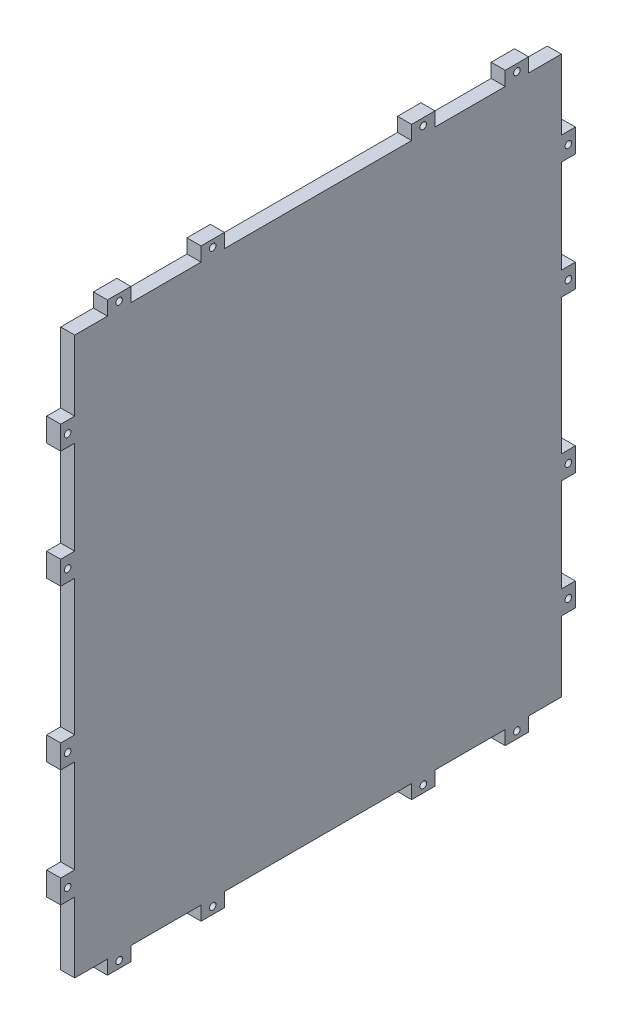
SolidWorks part; units mm, degrees
ref_plane "Plan de face" through (0, 0, 0) normal (0, 0, 1) x (1, 0, 0)
ref_plane "Plan de dessus" through (0, 0, 0) normal (0, 1, 0) x (1, 0, 0)
ref_plane "Plan de droite" through (0, 0, 0) normal (1, 0, 0) x (0, 0, -1)
sketch "Esquisse1" plane through (0, 0, 0) normal (1, 0, 0) x (0, 0, -1)
  line L0 (97.1531, 0) -> (-102.2664, 0) construction
  line L1 (-104, 119) -> (104, 119)
  line L2 (-104, 119) -> (-104, -119)
  line L3 (-104, -119) -> (104, -119)
  line L4 (104, 119) -> (104, -119)
  line L5 (0, 70.2098) -> (0, -91.4498) construction
  dimension "D1" = 238
  dimension "D2" = 208
  dimension "D3" = 104
  dimension "D4" = 119
extrude "Boss.-Extru.1" add sketch "Esquisse1" along normal blind 6
sketch "Esquisse3" plane through (6, 0, 0) normal (1, 0, 0) x (0, 0, -1)
  line L0 (-104, -119) -> (104, -119) construction
  line L1 (-90, -119) -> (-80, -119)
  line L2 (-90, -119) -> (-90, -125)
  line L3 (-90, -125) -> (-80, -125)
  line L4 (-80, -119) -> (-80, -125)
  line L5 (245.3741, 0) -> (-166.5298, 0) construction
  line L6 (-40, -119) -> (-50, -119)
  line L7 (-40, -119) -> (-40, -125)
  line L8 (-40, -125) -> (-50, -125)
  line L9 (-50, -119) -> (-50, -125)
  line L10 (0, 208.6671) -> (0, -232.3841) construction
  line L11 (-104, 119) -> (-104, -119) construction
  line L12 (110, -39) -> (110, -29)
  line L13 (-104, -89) -> (-110, -89)
  line L14 (-104, -89) -> (-104, -79)
  line L15 (-104, -79) -> (-110, -79)
  line L16 (-110, -89) -> (-110, -79)
  line L17 (-104, -39) -> (-110, -39)
  line L18 (-104, -39) -> (-104, -29)
  line L19 (-104, -29) -> (-110, -29)
  line L20 (-110, -39) -> (-110, -29)
  line L21 (104, -29) -> (110, -29)
  line L22 (104, -39) -> (104, -29)
  line L23 (104, -39) -> (110, -39)
  line L24 (110, -89) -> (110, -79)
  line L25 (104, -79) -> (110, -79)
  line L26 (104, -89) -> (104, -79)
  line L27 (104, -89) -> (110, -89)
  line L28 (50, -119) -> (50, -125)
  line L29 (40, -125) -> (50, -125)
  line L30 (40, -119) -> (40, -125)
  line L31 (40, -119) -> (50, -119)
  line L32 (80, -119) -> (80, -125)
  line L33 (90, -125) -> (80, -125)
  line L34 (90, -119) -> (90, -125)
  line L35 (90, -119) -> (80, -119)
  line L36 (90, 119) -> (80, 119)
  line L37 (90, 119) -> (90, 125)
  line L38 (90, 125) -> (80, 125)
  line L39 (80, 119) -> (80, 125)
  line L40 (40, 119) -> (50, 119)
  line L41 (40, 119) -> (40, 125)
  line L42 (40, 125) -> (50, 125)
  line L43 (50, 119) -> (50, 125)
  line L44 (104, 89) -> (110, 89)
  line L45 (104, 89) -> (104, 79)
  line L46 (104, 79) -> (110, 79)
  line L47 (110, 89) -> (110, 79)
  line L48 (104, 39) -> (110, 39)
  line L49 (104, 39) -> (104, 29)
  line L50 (104, 29) -> (110, 29)
  line L51 (-110, 39) -> (-110, 29)
  line L52 (-104, 29) -> (-110, 29)
  line L53 (-104, 39) -> (-104, 29)
  line L54 (-104, 39) -> (-110, 39)
  line L55 (-110, 89) -> (-110, 79)
  line L56 (-104, 79) -> (-110, 79)
  line L57 (-104, 89) -> (-104, 79)
  line L58 (-104, 89) -> (-110, 89)
  line L59 (110, 39) -> (110, 29)
  line L60 (-50, 119) -> (-50, 125)
  line L61 (-40, 125) -> (-50, 125)
  line L62 (-40, 119) -> (-40, 125)
  line L63 (-40, 119) -> (-50, 119)
  line L64 (-80, 119) -> (-80, 125)
  line L65 (-90, 125) -> (-80, 125)
  line L66 (-90, 119) -> (-90, 125)
  line L67 (-90, 119) -> (-80, 119)
  dimension "D1" = 14
  dimension "D2" = 10
  dimension "D3" = 6
  dimension "D4" = 6
  dimension "D5" = 10
  dimension "D6" = 30
  dimension "D7" = 10
  dimension "D8" = 10
  dimension "D9" = 6
  dimension "D10" = 6
  dimension "D11" = 30
  dimension "D12" = 40
extrude "Boss.-Extru.5" add sketch "Esquisse3" against normal blind 6
sketch "Esquisse4" plane through (6, 0, 0) normal (1, 0, 0) x (0, 0, -1)
  line L0 (0, 159.9693) -> (0, -141.7693) construction
  line L1 (244.9879, 0) -> (-172.9757, 0) construction
  line L2 (-104, 39) -> (-110, 39) construction
  line L3 (-110, 39) -> (-110, 29) construction
  line L4 (-110, 79) -> (-104, 79) construction
  line L5 (-110, 89) -> (-110, 79) construction
  line L6 (-80, 125) -> (-90, 125) construction
  line L7 (-90, 125) -> (-90, 119) construction
  line L8 (-40, 125) -> (-50, 125) construction
  line L9 (-40, 119) -> (-40, 125) construction
  circle A0 centre (-85, 122) radius 1.4
  circle A1 centre (-45, 122) radius 1.4
  circle A2 centre (-107, 84) radius 1.4
  circle A3 centre (-107, 34) radius 1.4
  circle A4 centre (107, 34) radius 1.4
  circle A5 centre (107, 84) radius 1.4
  circle A6 centre (45, 122) radius 1.4
  circle A7 centre (85, 122) radius 1.4
  circle A8 centre (85, -122) radius 1.4
  circle A9 centre (45, -122) radius 1.4
  circle A10 centre (107, -84) radius 1.4
  circle A11 centre (107, -34) radius 1.4
  circle A12 centre (-107, -34) radius 1.4
  circle A13 centre (-107, -84) radius 1.4
  circle A14 centre (-45, -122) radius 1.4
  circle A15 centre (-85, -122) radius 1.4
  dimension "D1" = 2.8
  dimension "D2" = 2.8
  dimension "D3" = 2.8
  dimension "D4" = 2.8
  dimension "D5" = 5
  dimension "D6" = 3
  dimension "D7" = 5
  dimension "D8" = 3
  dimension "D9" = 3
  dimension "D10" = 5
  dimension "D11" = 3
  dimension "D12" = 5
extrude "Enlèv. mat.-Extru.1" cut sketch "Esquisse4" against normal blind 6
equation "\"D3@Esquisse1\"=\"D2@Esquisse1\"/2"
equation "\"D4@Esquisse1\"=\"D1@Esquisse1\"/2"
